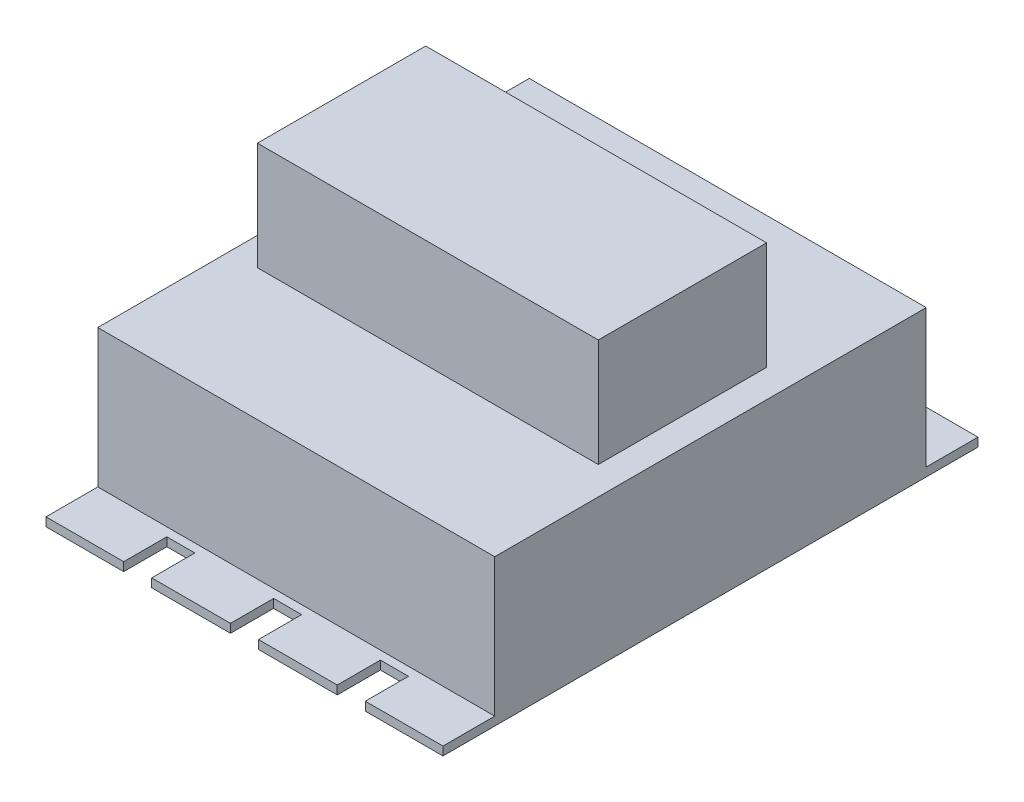
SolidWorks part; units mm, degrees
ref_plane "Спереди" through (0, 0, 0) normal (0, 0, 1) x (1, 0, 0)
ref_plane "Сверху" through (0, 0, 0) normal (0, 1, 0) x (1, 0, 0)
ref_plane "Справа" through (0, 0, 0) normal (1, 0, 0) x (0, 0, -1)
sketch "Эскиз1" plane through (0, 0, 0) normal (0, 1, 0) x (1, 0, 0)
  line L1 (0, 0) -> (92, 0)
  line L2 (0, 0) -> (0, 100)
  line L3 (0, 100) -> (92, 100)
  line L4 (92, 0) -> (92, 100)
  dimension "D1" = 92
  dimension "D2" = 100
extrude "Бобышка-Вытянуть1" add sketch "Эскиз1" along normal blind 34
sketch "Эскиз2" plane through (0, 34, 0) normal (0, 1, 0) x (1, 0, 0)
  line L0 (46, 100) -> (46, 0) construction
  line L1 (6.5, 69.5) -> (85.5, 69.5)
  line L2 (6.5, 69.5) -> (6.5, 30.5)
  line L3 (6.5, 30.5) -> (85.5, 30.5)
  line L4 (85.5, 69.5) -> (85.5, 30.5)
  line L5 (92, 100) -> (0, 100) construction
  line L6 (0, 0) -> (92, 0) construction
  line L7 (0, 50) -> (92, 50) construction
  line L8 (0, 100) -> (0, 0) construction
  line L9 (92, 0) -> (92, 100) construction
  point P16 (6.5, 50)
  point P17 (46, 69.5)
  dimension "D1" = 79
  dimension "D2" = 39
extrude "Бобышка-Вытянуть2" add sketch "Эскиз2" along normal blind 25
sketch "Эскиз3" plane through (0, 0, 0) normal (0, -1, 0) x (1, 0, 0)
  line L0 (-1019.8754, -50) -> (48980.1246, -50) construction
  line L1 (0, -100) -> (0, 0) construction
  line L2 (0, 0) -> (92, 0) construction
  line L3 (0, 12) -> (18, 12)
  line L4 (0, 12) -> (0, -112)
  line L6 (92, 12) -> (92, -112)
  line L7 (92, 0) -> (92, -100) construction
  line L8 (46, -1032.9821) -> (46, 48967.0179) construction
  line L9 (24.5, 12) -> (42.75, 12)
  line L11 (18, 12) -> (18, 2)
  line L12 (18, 2) -> (24.5, 2)
  line L13 (24.5, 12) -> (24.5, 2)
  line L15 (42.75, 12) -> (42.75, 2)
  line L16 (42.75, 2) -> (49.25, 2)
  line L17 (49.25, 12) -> (49.25, 2)
  line L19 (74, 12) -> (74, 2)
  line L20 (74, 2) -> (67.5, 2)
  line L21 (67.5, 12) -> (67.5, 2)
  line L22 (49.25, 12) -> (67.5, 12)
  line L23 (74, 12) -> (92, 12)
  line L24 (74, -112) -> (92, -112)
  line L25 (74, -112) -> (74, -102)
  line L26 (74, -102) -> (67.5, -102)
  line L27 (67.5, -112) -> (67.5, -102)
  line L28 (49.25, -112) -> (67.5, -112)
  line L29 (49.25, -112) -> (49.25, -102)
  line L30 (42.75, -102) -> (49.25, -102)
  line L31 (42.75, -112) -> (42.75, -102)
  line L32 (24.5, -112) -> (42.75, -112)
  line L33 (24.5, -112) -> (24.5, -102)
  line L34 (18, -102) -> (24.5, -102)
  line L35 (18, -112) -> (18, -102)
  line L36 (0, -112) -> (18, -112)
  point P4 (0, -50)
  point P14 (46, 0)
  point P24 (21.25, 2)
  point P27 (46, 2)
  point P32 (92, -50)
  point P45 (0, -50)
  dimension "D1" = 12
  dimension "D2" = 10
  dimension "D3" = 6.5
  dimension "D4" = 18
extrude "Бобышка-Вытянуть3" add sketch "Эскиз3" against normal blind 2
